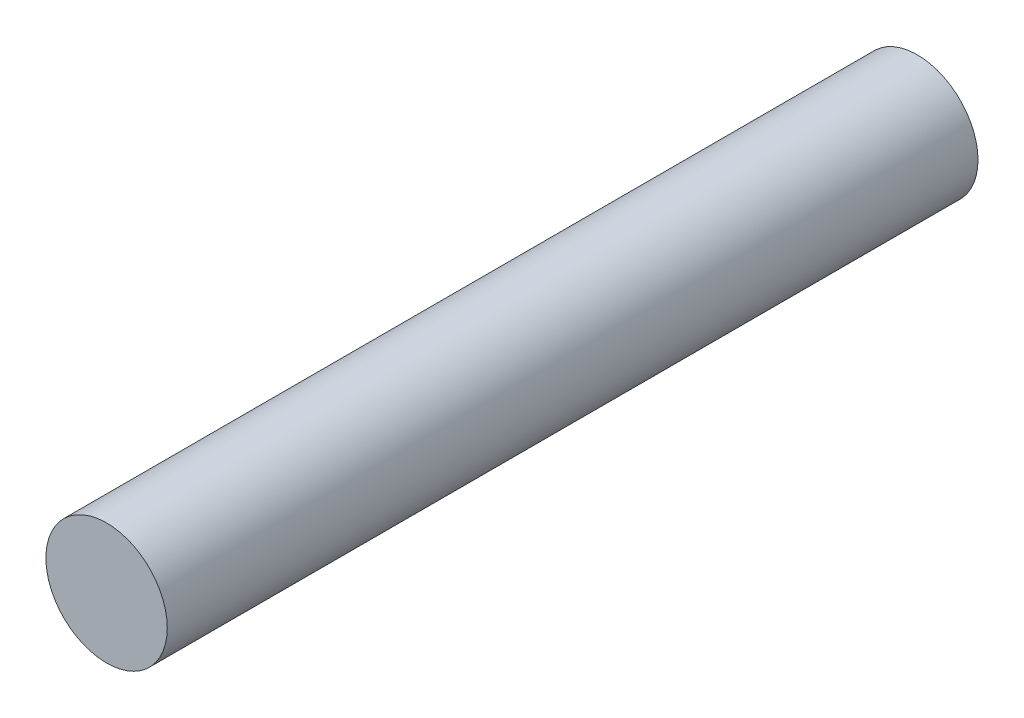
SolidWorks part; units mm, degrees
ref_plane "Ön Düzlem" through (0, 0, 0) normal (0, 0, 1) x (1, 0, 0)
ref_plane "Üst Düzlem" through (0, 0, 0) normal (0, 1, 0) x (1, 0, 0)
ref_plane "Sağ Düzlem" through (0, 0, 0) normal (1, 0, 0) x (0, 0, -1)
sketch "Çizim1" plane through (0, 0, 0) normal (0, 0, 1) x (1, 0, 0)
  circle A0 centre (-22.5509, 21.2254) radius 14.9721
extrude "Yükseklik-Ekstrüzyon1" add sketch "Çizim1" along normal blind 200
